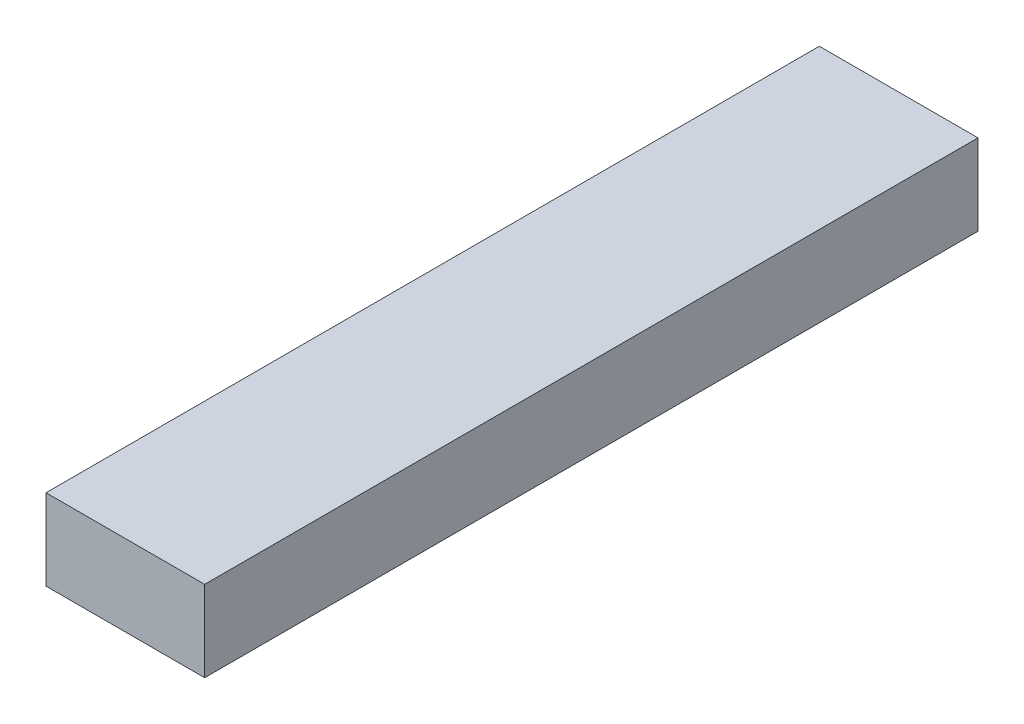
SolidWorks part; units mm, degrees
ref_plane "Front Plane" through (0, 0, 0) normal (0, 0, 1) x (1, 0, 0)
ref_plane "Top Plane" through (0, 0, 0) normal (0, 1, 0) x (1, 0, 0)
ref_plane "Right Plane" through (0, 0, 0) normal (1, 0, 0) x (0, 0, -1)
sketch "J1Header Sketch" plane through (0, 0, 0) normal (0, 1, 0) x (1, 0, 0)
  line L1 (0, 0) -> (15.1, 0)
  line L2 (0, 0) -> (0, 73.6)
  line L3 (0, 73.6) -> (15.1, 73.6)
  line L4 (15.1, 0) -> (15.1, 73.6)
  dimension "J1Header Width" = 15.1
  dimension "J1Header Length" = 73.6
extrude "J1 Header Extrude" add sketch "J1Header Sketch" along normal blind 7.7
